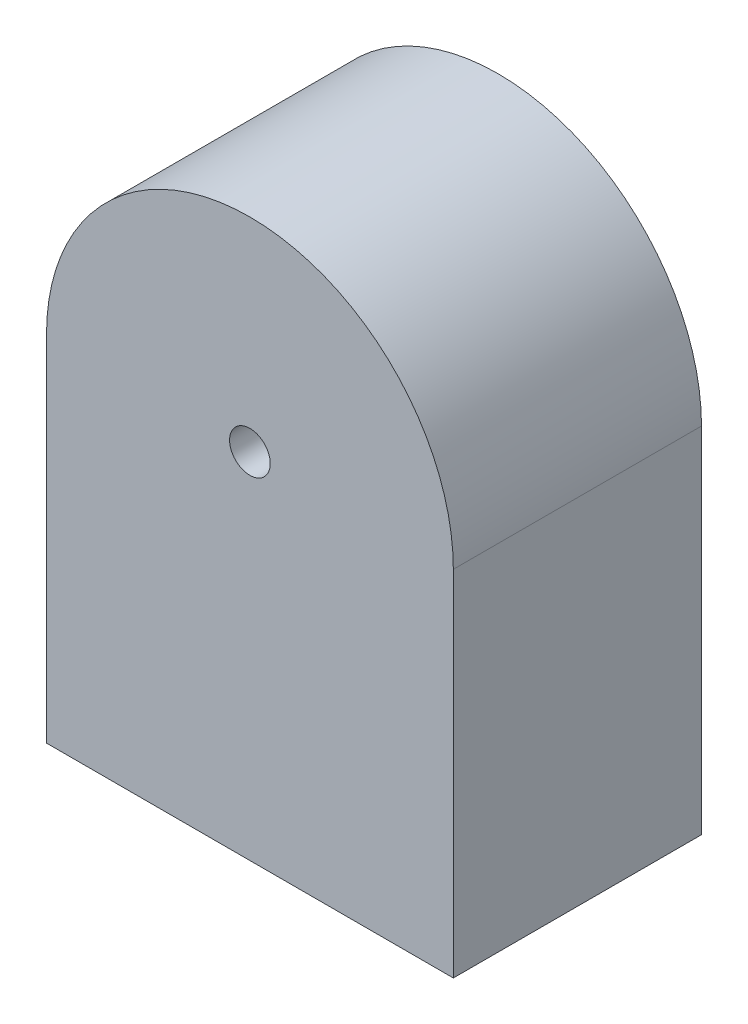
SolidWorks part; units mm, degrees
ref_plane "Front Plane" through (0, 0, 0) normal (0, 0, 1) x (1, 0, 0)
ref_plane "Top Plane" through (0, 0, 0) normal (0, 1, 0) x (1, 0, 0)
ref_plane "Right Plane" through (0, 0, 0) normal (1, 0, 0) x (0, 0, -1)
sketch "Sketch1" plane through (0, 0, 0) normal (0, 0, 1) x (1, 0, 0)
  line L0 (-15, 0) -> (-15, -26.1)
  line L1 (-15, -26.1) -> (15, -26.1)
  line L2 (15, -26.1) -> (15, 0)
  arc A0 (15, 0) -> (-15, 0) centre (0, 0) ccw
  circle A1 centre (0, 0) radius 1.5
  point P1 (0, 15)
  dimension "D1" = 15
  dimension "D3" = 3
  dimension "D2" = 41.1
extrude "Boss-Extrude1" add sketch "Sketch1" along normal blind 18.3
